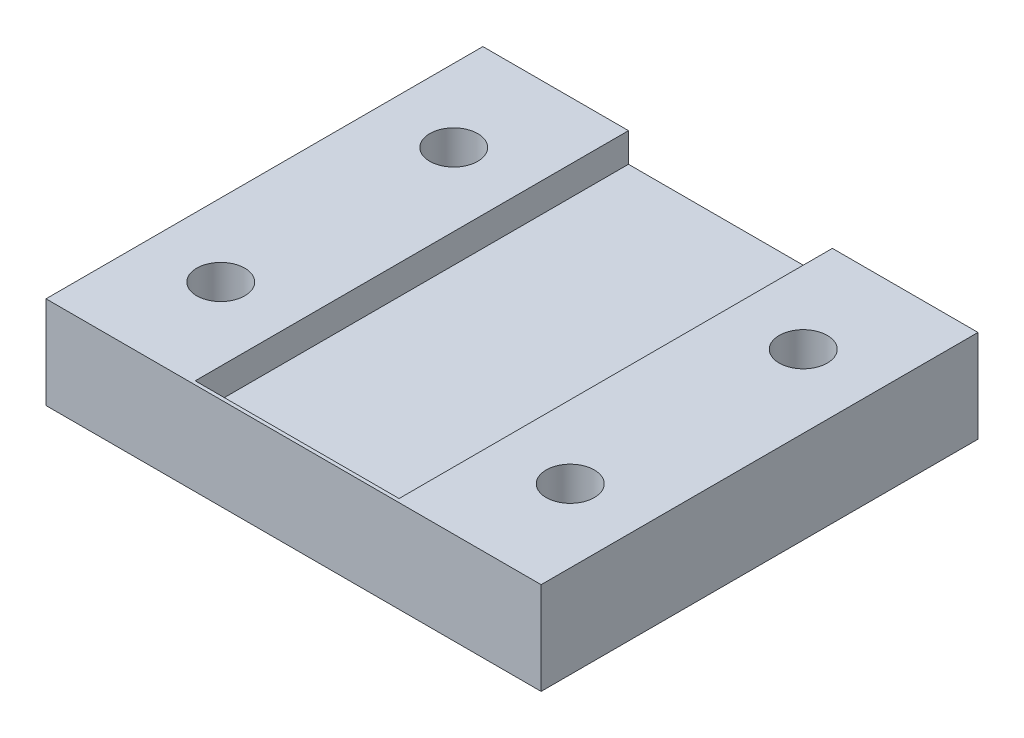
SolidWorks part; units mm, degrees
ref_plane "Front Plane" through (0, 0, 0) normal (0, 0, 1) x (1, 0, 0)
ref_plane "Top Plane" through (0, 0, 0) normal (0, 1, 0) x (1, 0, 0)
ref_plane "Right Plane" through (0, 0, 0) normal (1, 0, 0) x (0, 0, -1)
sketch "Sketch1" plane through (0, 0, 0) normal (0, 0, 1) x (1, 0, 0)
  line L1 (-17, 0) -> (17, 0)
  line L2 (-17, 0) -> (-17, 6.35)
  line L3 (-17, 6.35) -> (17, 6.35)
  line L4 (17, 0) -> (17, 6.35)
  point P4 (0, 0)
  dimension "D1" = 34
  dimension "D2" = 6.35
extrude "Boss-Extrude2" add sketch "Sketch1" along normal mid plane 30
sketch "Sketch3" plane through (0, 0, 0) normal (0, -1, 0) x (1, 0, 0)
  line L0 (-17, 0) -> (17, 0) construction
  line L1 (-17, 15) -> (-17, -15) construction
  line L2 (17, 15) -> (17, -15) construction
  line L3 (-12, 8) -> (12, 8) construction
  line L4 (-12, 8) -> (-12, -8) construction
  circle A0 centre (-12, 8) radius 1.65
  circle A1 centre (12, 8) radius 1.65
  circle A2 centre (-12, -8) radius 1.65
  circle A3 centre (12, -8) radius 1.65
  point P10 (-12, 0)
  point P11 (0, 8)
  dimension "D1" = 3.3
  dimension "D2" = 24
  dimension "D3" = 16
extrude "Cut-Extrude1" cut sketch "Sketch3" against normal up to surface (6.35 mm away) up to face at (0, 6.35, 0)
sketch "Sketch4" plane through (0, 6.35, 0) normal (0, 1, 0) x (1, 0, 0)
  line L0 (17, 15) -> (-17, 15) construction
  line L1 (-7, -14.755) -> (7, -14.755)
  line L2 (-7, -14.755) -> (-7, 15)
  line L3 (-7, 15) -> (7, 15)
  line L4 (7, -14.755) -> (7, 15)
  line L5 (0, -3.4925) -> (0, 3.4925) construction
  point P8 (0, 15)
  dimension "D1" = 14
extrude "Cut-Extrude2" cut sketch "Sketch4" against normal blind 2
